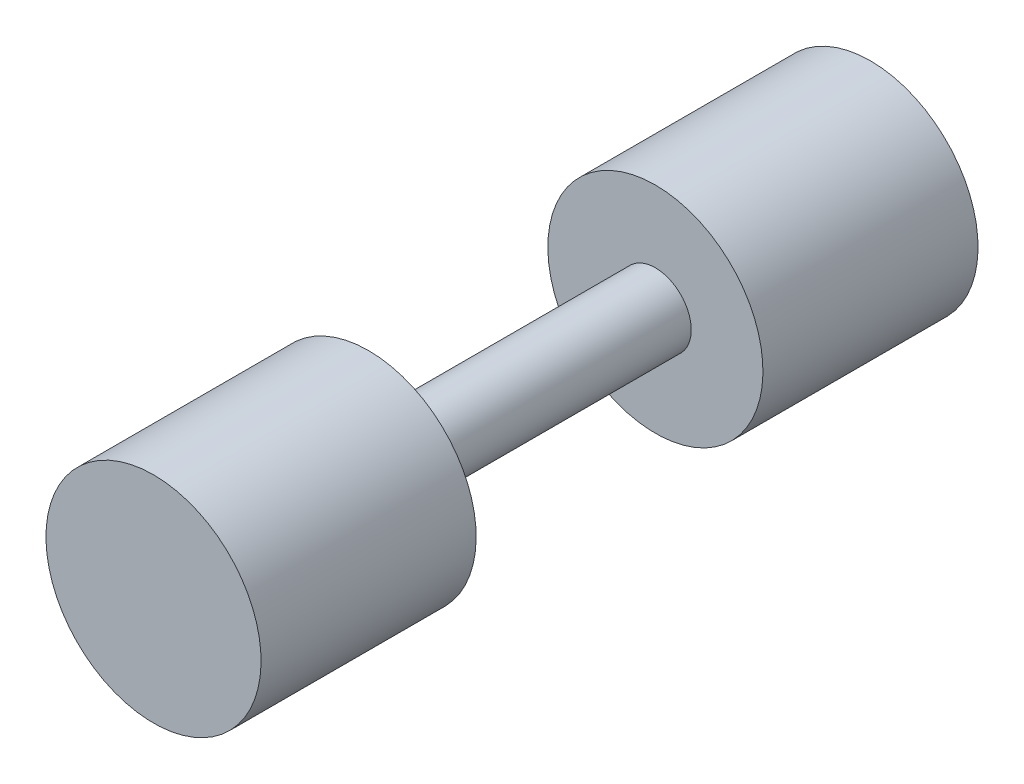
SolidWorks part; units mm, degrees
material "6061 Alloy"
ref_plane "Front Plane" through (0, 0, 0) normal (0, 0, 1) x (1, 0, 0)
ref_plane "Top Plane" through (0, 0, 0) normal (0, 1, 0) x (1, 0, 0)
ref_plane "Right Plane" through (0, 0, 0) normal (1, 0, 0) x (0, 0, -1)
sketch "Sketch1" plane through (0, 0, 0) normal (1, 0, 0) x (0, 0, -1)
  line L0 (63.5, 0) -> (-63.5, 0)
  line L1 (-63.5, 0) -> (-63.5, 19.05)
  line L2 (-63.5, 19.05) -> (-25.4, 19.05)
  line L3 (-25.4, 19.05) -> (-25.4, 6.35)
  line L4 (-25.4, 6.35) -> (25.4, 6.35)
  line L5 (25.4, 6.35) -> (25.4, 19.05)
  line L6 (25.4, 19.05) -> (63.5, 19.05)
  line L7 (63.5, 19.05) -> (63.5, 0)
  point P4 (0, 0)
  dimension "D1" = 38.1
  dimension "D2" = 19.05
  dimension "D3" = 6.35
  dimension "D4" = 127
  dimension "D5" = 50.8
revolve "Revolve1" add sketch "Sketch1" angle 360 about L0
